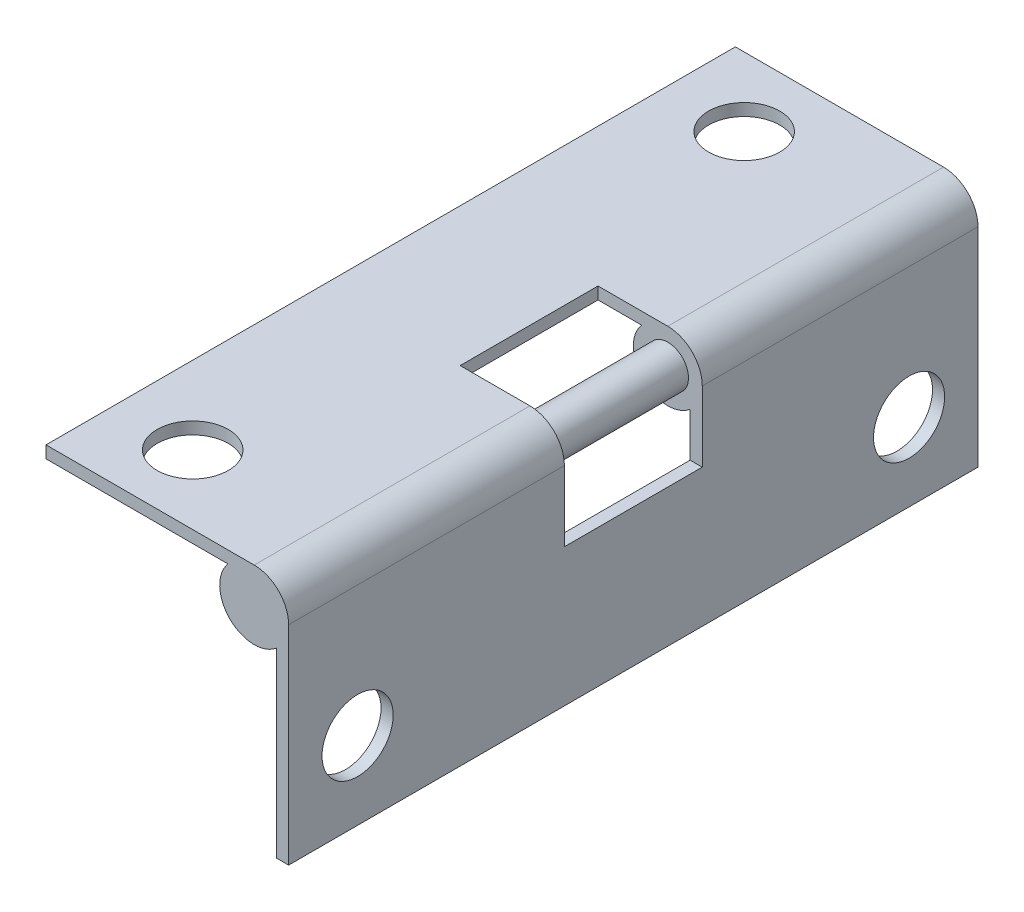
SolidWorks part; units mm, degrees
ref_plane "Front Plane" through (0, 0, 0) normal (0, 0, 1) x (1, 0, 0)
ref_plane "Top Plane" through (0, 0, 0) normal (0, 1, 0) x (1, 0, 0)
ref_plane "Right Plane" through (0, 0, 0) normal (1, 0, 0) x (0, 0, -1)
sketch "Sketch1" plane through (0, 0, 0) normal (0, 0, 1) x (1, 0, 0)
  line L0 (0, 1.5875) -> (-9.5885, 1.5875)
  line L1 (-9.5885, 1.5875) -> (-9.5885, 1.0287)
  line L2 (-9.5885, 1.0287) -> (-1.2091, 1.0287)
  line L3 (1.5875, 0) -> (1.5875, -9.5885)
  line L4 (1.5875, -9.5885) -> (1.0287, -9.5885)
  line L5 (1.0287, -9.5885) -> (1.0287, -1.2091)
  arc A0 (-1.2091, 1.0287) -> (1.0287, -1.2091) centre (0, 0) ccw
  arc A1 (1.5875, 0) -> (0, 1.5875) centre (0, 0) ccw
  dimension "D1" = 3.175
  dimension "D2" = 0.5588
  dimension "D3" = 11.176
  dimension "D4" = 11.176
extrude "Boss-Extrude1" add sketch "Sketch1" along normal blind 31.75
sketch "Sketch2" plane through (0, 1.5875, 0) normal (0, 1, 0) x (1, 0, 0)
  line L0 (-6.0071, 0) -> (-6.0071, -31.75) construction
  line L1 (0, 0) -> (-9.5885, 0) construction
  line L2 (0, -31.75) -> (-9.5885, -31.75) construction
  line L3 (-9.5885, -31.75) -> (-9.5885, 0) construction
  line L4 (1.5875, -31.75) -> (1.5875, 0) construction
  line L5 (-3.2131, -12.7) -> (1.5875, -12.7)
  line L6 (-3.2131, -12.7) -> (-3.2131, -19.05)
  line L7 (-3.2131, -19.05) -> (1.5875, -19.05)
  line L8 (1.5875, -12.7) -> (1.5875, -19.05)
  line L9 (-3.2131, -12.7) -> (1.5875, -19.05) construction
  line L10 (-3.2131, -19.05) -> (1.5875, -12.7) construction
  line L11 (1.5875, -31.75) -> (1.5875, 0)
  circle A0 centre (-6.0071, -3.175) radius 1.6383
  circle A1 centre (-6.0071, -28.575) radius 1.6383
  point P16 (-0.8128, -15.875)
  line M5 (0, -31.75) -> (0, 0)
  dimension "D1" = 3.2766
  dimension "D2" = 3.5814
  dimension "D3" = 3.175
  dimension "D4" = 25.4
  dimension "D5" = 6.35
  dimension "D6" = 4.8006
  dimension "D7" = 12.7
extrude "Cut-Extrude1" cut sketch "Sketch2" against normal blind 4.826 contours A1 | A0 | L6 L7 L5 M5 | L8 L5 L7 M5
sketch "Sketch3" plane through (1.5875, 0, 0) normal (1, 0, 0) x (0, 0, -1)
  line L0 (-31.75, -6.0071) -> (0, -6.0071) construction
  line L1 (-31.75, -9.5885) -> (-31.75, 0) construction
  line L2 (0, -9.5885) -> (0, 0) construction
  line L3 (-31.75, -9.5885) -> (0, -9.5885) construction
  circle A0 centre (-28.575, -6.0071) radius 1.6383
  circle A1 centre (-3.175, -6.0071) radius 1.6383
  dimension "D1" = 3.2766
  dimension "D2" = 3.5814
  dimension "D3" = 3.175
  dimension "D4" = 25.4
extrude "Cut-Extrude2" cut sketch "Sketch3" against normal through all
sketch "Sketch4" plane through (0, 0, 19.05) normal (0, 0, -1) x (-1, 0, 0)
  circle A0 centre (0, 0) radius 0.9525
  dimension "D1" = 1.905
extrude "Boss-Extrude2" add sketch "Sketch4" along normal up to next
equation "\"D4@Sketch1\"=\"D3@Sketch1\""
equation "\"D6@Sketch2\"=.25-.122/2"
equation "\"D7@Sketch2\"=\"D4@Sketch2\"/2"
